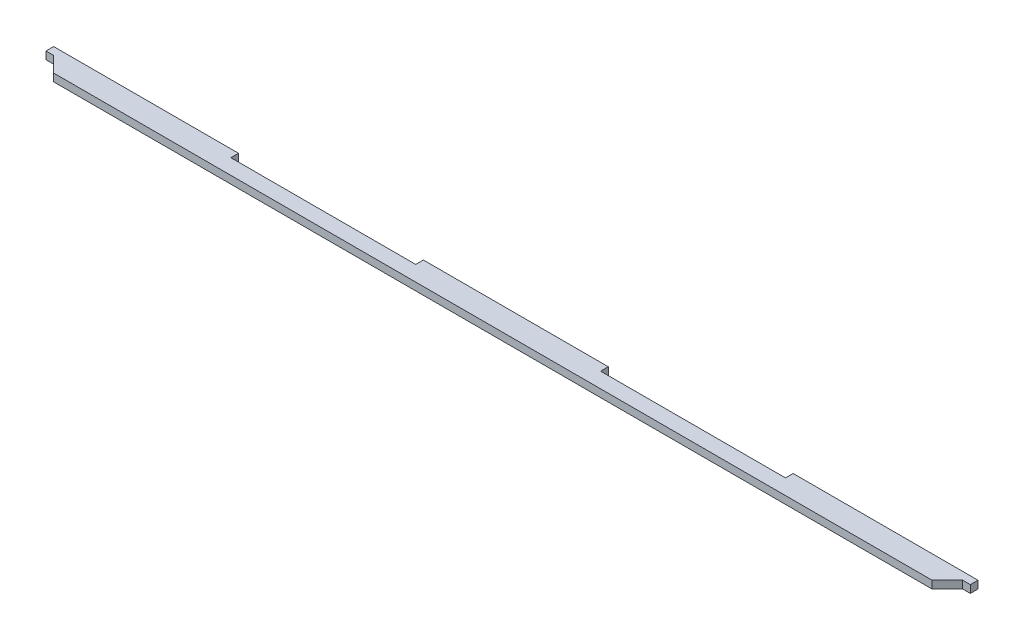
SolidWorks part; units mm, degrees
ref_plane "Front Plane" through (0, 0, 0) normal (0, 0, 1) x (1, 0, 0)
ref_plane "Top Plane" through (0, 0, 0) normal (0, 1, 0) x (1, 0, 0)
ref_plane "Right Plane" through (0, 0, 0) normal (1, 0, 0) x (0, 0, -1)
sketch "Sketch1" plane through (0, 0, 0) normal (0, 1, 0) x (1, 0, 0)
  line L1 (-181.15, 4.0789) -> (-108.69, 4.0789)
  line L2 (-181.15, 4.0789) -> (-181.15, 1.0789)
  line L3 (-172.15, -4.9211) -> (172.15, -4.9211)
  line L4 (181.15, 4.0789) -> (181.15, 1.0789)
  line L6 (-181.15, 1.0789) -> (-178.15, 1.0789)
  line L7 (-36.23, 4.0789) -> (36.23, 4.0789)
  line L9 (108.69, 4.0789) -> (181.15, 4.0789)
  line L10 (-108.69, 4.0789) -> (-108.69, 1.0789)
  line L11 (-36.23, 4.0789) -> (-36.23, 1.0789)
  line L12 (36.23, 4.0789) -> (36.23, 1.0789)
  line L13 (108.69, 4.0789) -> (108.69, 1.0789)
  line L14 (-108.69, 1.0789) -> (-36.23, 1.0789)
  line L16 (36.23, 1.0789) -> (108.69, 1.0789)
  line L18 (178.15, 1.0789) -> (181.15, 1.0789)
  line L19 (-178.15, 1.0789) -> (-172.15, -4.9211)
  line L20 (178.15, 1.0789) -> (172.15, -4.9211)
  point P0 (0, 0)
  dimension "D1" = 362.3
  dimension "D3" = 3
extrude "Boss-Extrude1" add sketch "Sketch1" along normal blind 3
